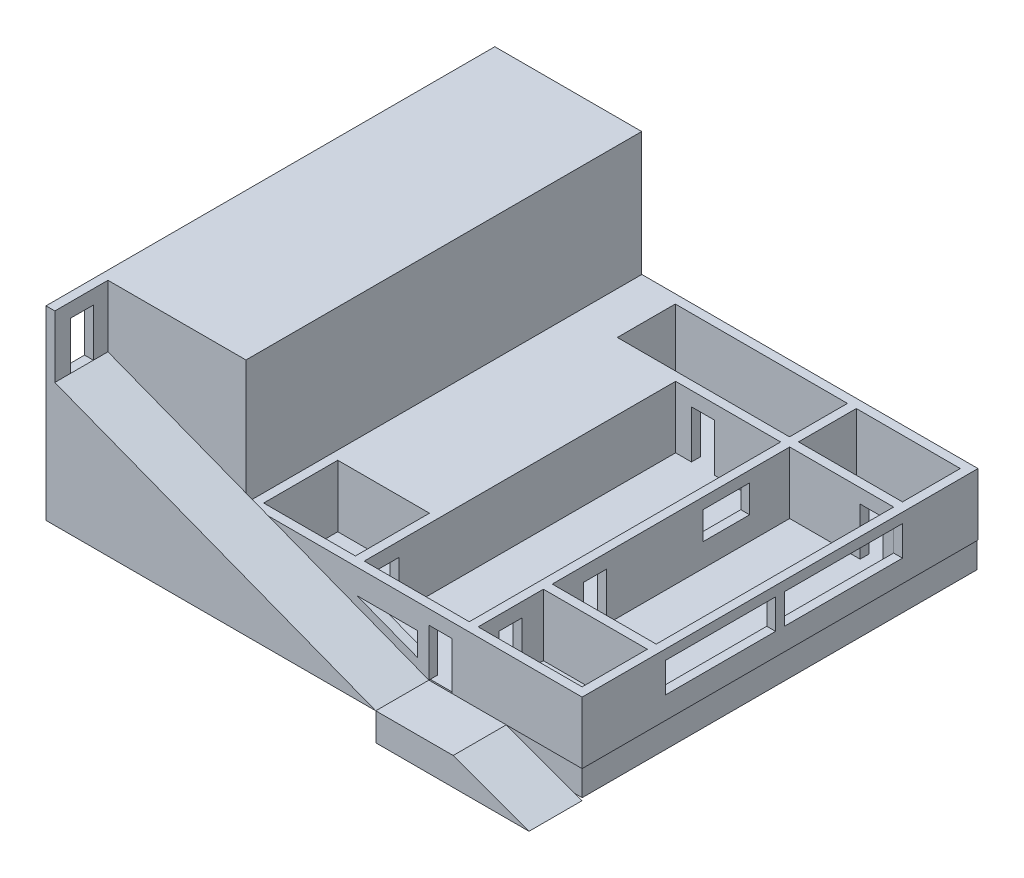
SolidWorks part; units mm, degrees
ref_plane "Plano frontal" through (0, 0, 0) normal (0, 0, 1) x (1, 0, 0)
ref_plane "Plano superior" through (0, 0, 0) normal (0, 1, 0) x (1, 0, 0)
ref_plane "Plano direito" through (0, 0, 0) normal (1, 0, 0) x (0, 0, -1)
sketch "Esboço2" plane through (0, 0, 0) normal (0, 1, 0) x (1, 0, 0)
  line L1 (76.0864, -36.8492) -> (64.3363, -36.8492)
  line L2 (76.0864, -36.8492) -> (76.0864, -29.4763)
  line L3 (76.0864, -29.4763) -> (64.3363, -29.4763)
  line L4 (64.3363, -36.8492) -> (64.3363, -29.4763)
  line L6 (77.0864, -37.8492) -> (77.0864, 6.8856)
  line L7 (63.3363, -36.8492) -> (51.4645, -36.8492)
  line L8 (76.0864, -28.4763) -> (64.3363, -28.4763)
  line L9 (76.0864, -28.4763) -> (76.0864, -1.6449)
  line L10 (76.0864, -1.6449) -> (64.3363, -1.6449)
  line L11 (64.3363, -28.4763) -> (64.3363, -1.6449)
  line L12 (63.3363, -36.8492) -> (63.3363, -1.6627)
  line L13 (63.3363, -1.6627) -> (51.4645, -1.6627)
  line L14 (51.4645, -36.8492) -> (51.4645, -1.6627)
  line L15 (76.0864, -0.6449) -> (64.3363, -0.6449)
  line L16 (76.0864, -0.6449) -> (76.0864, 5.8856)
  line L17 (76.0864, 5.8856) -> (64.3363, 5.8856)
  line L18 (64.3363, -0.6449) -> (64.3363, 5.8856)
  line L19 (63.3363, -0.6627) -> (43.8802, -0.6627)
  line L20 (63.3363, -0.6627) -> (63.3363, 5.8856)
  line L21 (63.3363, 5.8856) -> (43.8802, 5.8856)
  line L22 (43.8802, -0.6627) -> (43.8802, 5.8856)
  line L23 (50.4645, -36.8492) -> (40.1001, -36.8492)
  line L24 (50.4645, -36.8492) -> (50.4645, -28.4763)
  line L25 (50.4645, -28.4763) -> (40.1001, -28.4763)
  line L26 (40.1001, -36.8492) -> (40.1001, -28.4763)
  line L27 (77.0864, -37.8492) -> (39.1001, -37.8492)
  line L28 (39.1001, -37.8492) -> (39.1001, 6.8856)
  line L29 (39.1001, 6.8856) -> (77.0864, 6.8856)
  dimension "D3" = 1
  dimension "D4" = 1
  dimension "D5" = 1
  dimension "D6" = 1
  dimension "D7" = 1
  dimension "D8" = 1
  dimension "D9" = 1
  dimension "D10" = 1
  dimension "D11" = 1
extrude "Ressalto-extrusão3" add sketch "Esboço2" along normal blind 7
sketch "Esboço3" plane through (0, 0, 37.8492) normal (0, 0, 1) x (1, 0, 0)
  line L1 (62.3675, -0.017) -> (59.7675, -0.017)
  line L2 (62.3675, -0.017) -> (62.3675, 5.383)
  line L3 (62.3675, 5.383) -> (59.7675, 5.383)
  line L4 (59.7675, -0.017) -> (59.7675, 5.383)
  dimension "D1" = 2.6
  dimension "D2" = 5.4
extrude "Corte-extrusão1" cut sketch "Esboço3" against normal blind 7
sketch "Esboço4" plane through (51.4645, 0, 0) normal (1, 0, 0) x (0, 0, -1)
  line L0 (-1.6627, 0) -> (-36.8492, 0) construction
  line L1 (-35.5119, 0) -> (-32.9119, 0)
  line L2 (-35.5119, 0) -> (-35.5119, 5.4)
  line L3 (-35.5119, 5.4) -> (-32.9119, 5.4)
  line L4 (-32.9119, 0) -> (-32.9119, 5.4)
  dimension "D1" = 2.6
  dimension "D2" = 5.4
extrude "Corte-extrusão2" cut sketch "Esboço4" against normal blind 7
sketch "Esboço5" plane through (64.3363, 0, 0) normal (1, 0, 0) x (0, 0, -1)
  line L0 (-1.6449, 0) -> (-28.4763, 0) construction
  line L1 (-24.9436, 0) -> (-22.3436, 0)
  line L2 (-24.9436, 0) -> (-24.9436, 5.4)
  line L3 (-24.9436, 5.4) -> (-22.3436, 5.4)
  line L4 (-22.3436, 0) -> (-22.3436, 5.4)
  line L5 (-29.4763, 0) -> (-36.8492, 0) construction
  line L6 (-34.4882, 0) -> (-31.8882, 0)
  line L7 (-34.4882, 0) -> (-34.4882, 5.4)
  line L8 (-34.4882, 5.4) -> (-31.8882, 5.4)
  line L9 (-31.8882, 0) -> (-31.8882, 5.4)
  dimension "D1" = 2.6
  dimension "D2" = 5.4
  dimension "D3" = 5.4
  dimension "D4" = 2.6
extrude "Corte-extrusão3" cut sketch "Esboço5" against normal blind 7
sketch "Esboço6" plane through (0, 0, 1.6627) normal (0, 0, 1) x (1, 0, 0)
  line L0 (63.3363, 0) -> (51.4645, 0) construction
  line L1 (53.2542, 0) -> (55.8542, 0)
  line L2 (53.2542, 0) -> (53.2542, 5.4)
  line L3 (53.2542, 5.4) -> (55.8542, 5.4)
  line L4 (55.8542, 0) -> (55.8542, 5.4)
  line L5 (76.0864, 0) -> (64.3363, 0) construction
  line L6 (72.2942, 0) -> (74.8942, 0)
  line L7 (72.2942, 0) -> (72.2942, 5.4)
  line L8 (72.2942, 5.4) -> (74.8942, 5.4)
  line L9 (74.8942, 0) -> (74.8942, 5.4)
  dimension "D1" = 2.6
  dimension "D2" = 2.6
  dimension "D3" = 5.4
  dimension "D4" = 5.4
extrude "Corte-extrusão4" cut sketch "Esboço6" against normal blind 7
sketch "Esboço7" plane through (77.0864, 0, 0) normal (1, 0, 0) x (0, 0, -1)
  line L1 (-28.4411, 5.8829) -> (-15.9844, 5.8829)
  line L2 (-28.4411, 5.8829) -> (-28.4411, 2.5)
  line L3 (-28.4411, 2.5) -> (-15.9844, 2.5)
  line L4 (-1.6495, 5.8829) -> (-1.6495, 2.5)
  line L5 (-15.9844, 5.8829) -> (-15.9844, 2.5)
  line L7 (-14.9844, 2.5) -> (-14.9844, 5.8829)
  line L9 (-14.9844, 2.5) -> (-1.6495, 2.5)
  line L10 (-14.9844, 5.8829) -> (-1.6495, 5.8829)
  dimension "D2" = 1
extrude "Corte-extrusão5" cut sketch "Esboço7" against normal blind 7
sketch "Esboço8" plane through (64.3363, 0, 0) normal (1, 0, 0) x (0, 0, -1)
  line L1 (-11.4582, 5.7559) -> (-6.169, 5.7559)
  line L2 (-11.4582, 5.7559) -> (-11.4582, 2.6266)
  line L3 (-11.4582, 2.6266) -> (-6.169, 2.6266)
  line L4 (-6.169, 5.7559) -> (-6.169, 2.6266)
extrude "Corte-extrusão6" cut sketch "Esboço8" against normal blind 7 contours L2 L1 L4 L3
sketch "Esboço9" plane through (0, 0, 0) normal (0, 1, 0) x (1, 0, 0)
  line L0 (39.1001, -37.8492) -> (39.1001, 6.8856)
  line L1 (39.1001, -37.8492) -> (22.5036, -37.8492)
  line L3 (39.1001, 6.8685) -> (22.5036, 6.8685)
  line L4 (22.5036, -37.8492) -> (22.5036, 6.8685)
extrude "Ressalto-extrusão4" add sketch "Esboço9" along normal blind 21 contours L4 L1 L0 L3
sketch "Esboço10" plane through (0, 0, 37.8492) normal (0, 0, 1) x (1, 0, 0)
  line L1 (22.5036, 21) -> (23.5036, 21)
  line L2 (22.5036, 21) -> (22.5036, 14)
  line L3 (22.5036, 14) -> (23.5036, 14)
  line L4 (23.5036, 21) -> (23.5036, 14)
  dimension "D1" = 7
  dimension "D2" = 1
extrude "Ressalto-extrusão5" add sketch "Esboço10" along normal blind 6
sketch "Esboço11" plane through (0, 0, 37.8492) normal (0, 0, 1) x (1, 0, 0)
  line L0 (23.5036, 14) -> (59.7675, 0)
  line L1 (62.3675, 0) -> (68.5153, 0)
  line L2 (62.3675, 0) -> (77.0864, 0) construction
  line L3 (68.5153, 0) -> (77.0864, -3.1333)
  line L4 (22.5036, 14) -> (22.5036, 0)
  line L5 (22.5036, 0) -> (68.5153, 0)
  line L6 (77.0864, -3.1333) -> (59.7675, -3.1333)
  line L7 (22.5036, 14) -> (23.5036, 14)
  line L8 (59.7675, -3.1333) -> (59.7675, 0)
  line L9 (59.7675, 0) -> (68.5153, 0)
  line M2 (23.5036, 14) -> (22.5036, 14)
  line M3 (22.5036, 14) -> (22.5036, 0)
  line M4 (22.5036, 0) -> (59.7675, 0)
  line M8 (62.3675, 0) -> (77.0864, 0)
  line M10 (77.0864, 7) -> (39.1001, 7)
  line M11 (39.1001, 7) -> (39.1001, 21)
sketch "Esboço12" plane through (23.5036, 0, 0) normal (1, 0, 0) x (0, 0, -1)
  line L1 (-42.0938, 14) -> (-39.4938, 14)
  line L2 (-42.0938, 14) -> (-42.0938, 19.4)
  line L3 (-42.0938, 19.4) -> (-39.4938, 19.4)
  line L4 (-39.4938, 14) -> (-39.4938, 19.4)
  dimension "D1" = 2.6
  dimension "D2" = 5.4
extrude "Corte-extrusão7" cut sketch "Esboço12" against normal blind 6
extrude "Ressalto-extrusão10" add sketch "Esboço11" along normal up to surface (6 mm away) contours L0 M2 M3 M4 M10 M11 | L8 L6 L3 L5 M8 | L0 M11 M10 up to face at (23.0036, 17.5, 43.8492)
sketch "Esboço14" plane through (0, 0, 0) normal (0, 1, 0) x (1, 0, 0)
  line L0 (76.9354, -37.6919) -> (22.5036, -37.6919)
  line L9 (22.5036, -37.6919) -> (22.5036, 6.9308)
  line L11 (22.5036, 6.9308) -> (76.9354, 6.9308)
  line L12 (76.9354, 6.9308) -> (76.9354, -37.6919)
  line L13 (22.5036, -43.8492) -> (22.5036, 6.8685) construction
extrude "Ressalto-extrusão21" add sketch "Esboço14" against normal blind 3 contours L12 L0 L9 L11
sketch "Esboço15" plane through (0, 0, 37.8492) normal (0, 0, 1) x (1, 0, 0)
  line L0 (51.6403, 4.2095) -> (58.4766, 1.5703)
  line L5 (41.6355, 7) -> (59.7675, 0) construction
  line L6 (58.4766, 1.5703) -> (58.4766, 4.2095)
  line L7 (58.4766, 4.2095) -> (51.6403, 4.2095)
  point P2 (51.6312, 4.786)
  point P4 (0, 0)
  dimension "D1" = 1
extrude "Corte-extrusão8" cut sketch "Esboço15" against normal blind 10
